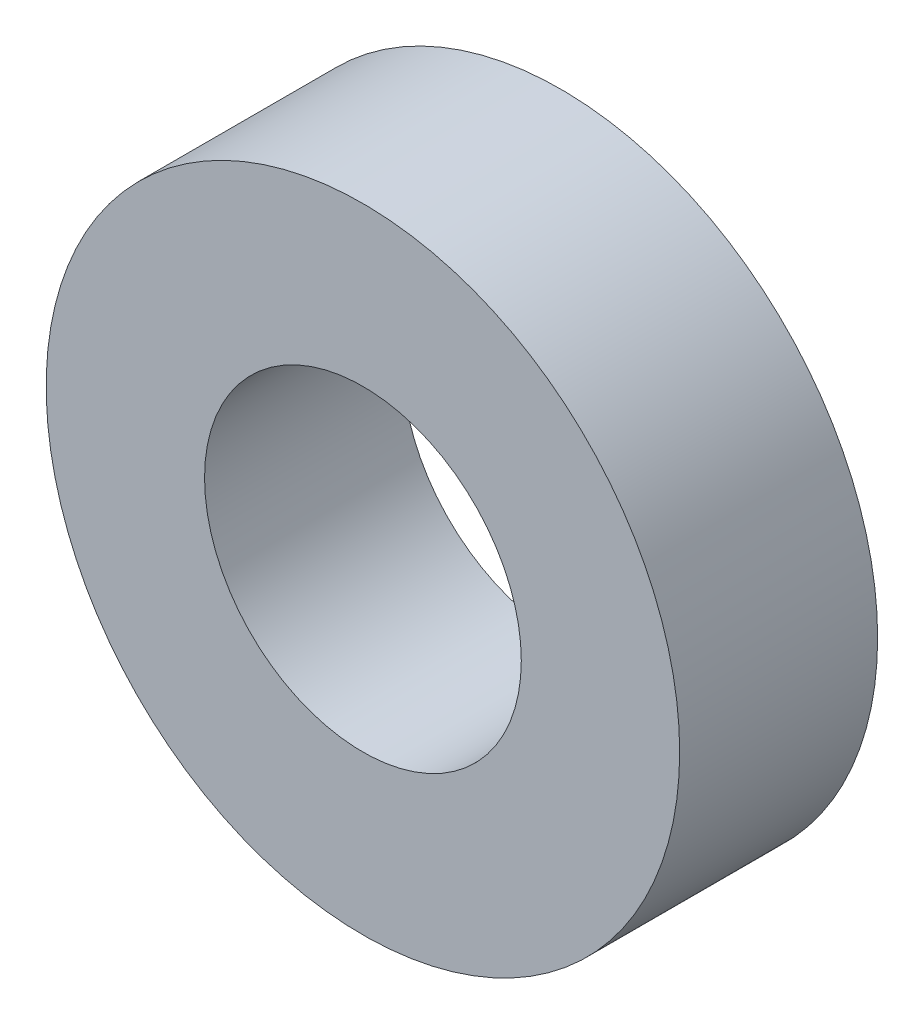
SolidWorks part; units mm, degrees
material "不锈钢 (铁素体)"
ref_plane "前视基准面" through (0, 0, 0) normal (0, 0, 1) x (1, 0, 0)
ref_plane "上视基准面" through (0, 0, 0) normal (0, 1, 0) x (1, 0, 0)
ref_plane "右视基准面" through (0, 0, 0) normal (1, 0, 0) x (0, 0, -1)
sketch "草图1" plane through (0, 0, 0) normal (0, 0, 1) x (1, 0, 0)
  circle A0 centre (0, 0) radius 4
  circle A1 centre (0, 0) radius 8
  dimension "D1" = 8
  dimension "D2" = 16
extrude "凸台-拉伸1" add sketch "草图1" along normal blind 5
